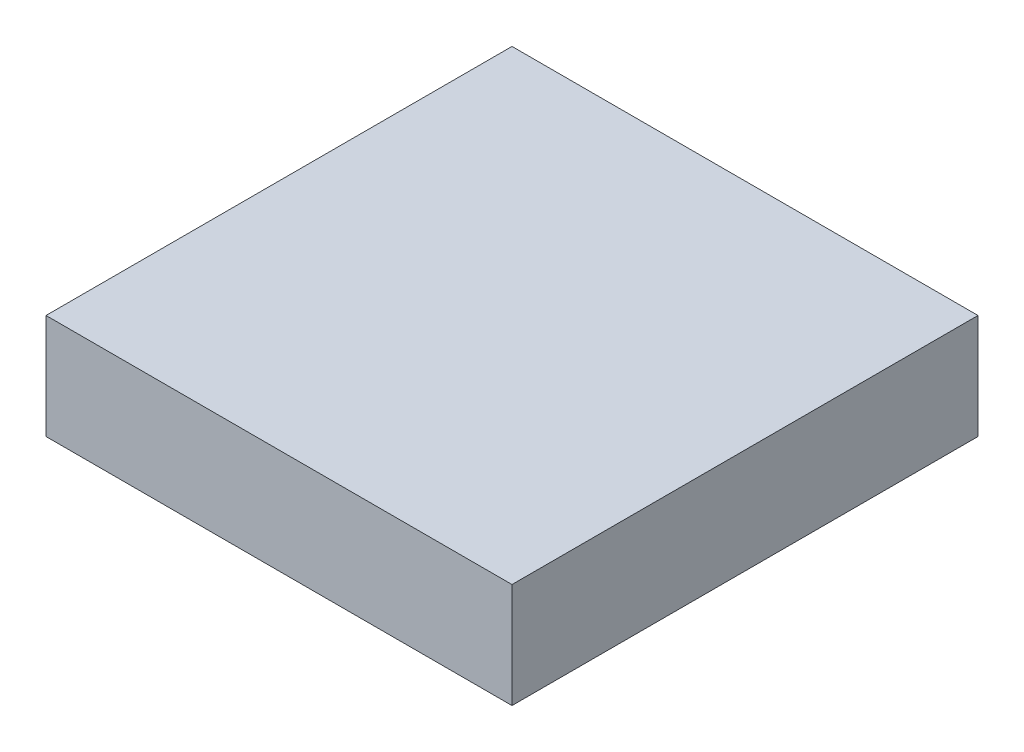
SolidWorks part; units mm, degrees
ref_plane "Front Plane" through (0, 0, 0) normal (0, 0, 1) x (1, 0, 0)
ref_plane "Top Plane" through (0, 0, 0) normal (0, 1, 0) x (1, 0, 0)
ref_plane "Right Plane" through (0, 0, 0) normal (1, 0, 0) x (0, 0, -1)
sketch "Sketch1" plane through (0, 0, 0) normal (0, 1, 0) x (1, 0, 0)
  line L1 (2, 2) -> (-2, 2)
  line L2 (2, 2) -> (2, -2)
  line L3 (2, -2) -> (-2, -2)
  line L4 (-2, 2) -> (-2, -2)
  line L5 (2, 2) -> (-2, -2) construction
  line L6 (2, -2) -> (-2, 2) construction
  point P0 (0, 0)
  dimension "D1" = 4
extrude "Boss-Extrude1" add sketch "Sketch1" along normal blind 0.9
